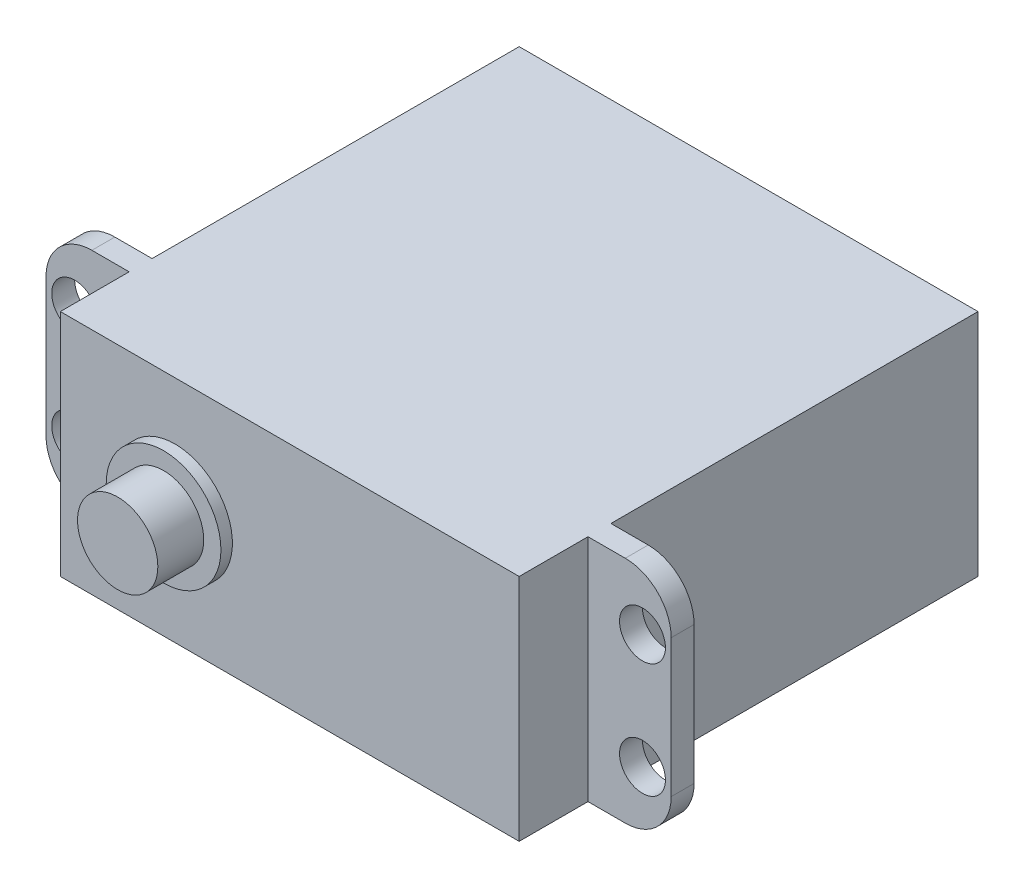
SolidWorks part; units mm, degrees
ref_plane "Front Plane" through (0, 0, 0) normal (0, 0, 1) x (1, 0, 0)
ref_plane "Top Plane" through (0, 0, 0) normal (0, 1, 0) x (1, 0, 0)
ref_plane "Right Plane" through (0, 0, 0) normal (1, 0, 0) x (0, 0, -1)
sketch "Sketch1" plane through (0, 0, 0) normal (0, 0, 1) x (1, 0, 0)
  line L1 (-20, -10) -> (20, -10)
  line L2 (-20, -10) -> (-20, 10)
  line L3 (-20, 10) -> (20, 10)
  line L4 (20, -10) -> (20, 10)
  line L5 (-20, -10) -> (20, 10) construction
  line L6 (-20, 10) -> (20, -10) construction
  point P0 (0, 0)
extrude "Boss-Extrude2" add sketch "Sketch1" along normal blind 40 contours L3 L4 L1 L2
sketch "Sketch2" plane through (20, 0, 0) normal (1, 0, 0) x (0, 0, -1)
  line L0 (-40, -10) -> (-34, -10)
  line L1 (-40, -10) -> (0, -10) construction
  line L2 (-34, -10) -> (-34, 10)
  line L3 (-40, 10) -> (0, 10) construction
  line L4 (-34, 10) -> (-32, 10)
  line L5 (-32, 10) -> (-32, -10)
  line L6 (-32, -10) -> (-34, -10)
extrude "Boss-Extrude3" add sketch "Sketch2" along normal blind 7.25 contours L2 L4 L5 L6
sketch "Sketch3" plane through (0, 0, 34) normal (0, 0, 1) x (1, 0, 0)
  circle A0 centre (24.75, -4.9991) radius 2
  circle A1 centre (24.75, 4.9994) radius 2
extrude "Cut-Extrude1" cut sketch "Sketch3" against normal blind 2 contours A1 | A0
fillet "Fillet3" radius 4 2 edges at (27.25, 10, 33) (27.25, -10, 33)
sketch "Sketch4" plane through (-20, 0, 0) normal (-1, 0, 0) x (0, 0, 1)
  line L0 (40, -10) -> (34, -10)
  line L1 (40, -10) -> (0, -10) construction
  line L2 (34, -10) -> (34, 10)
  line L3 (40, 10) -> (0, 10) construction
  line L4 (34, 10) -> (32, 10)
  line L5 (32, 10) -> (32, -10)
  line L6 (32, -10) -> (34, -10)
extrude "Boss-Extrude4" add sketch "Sketch4" along normal blind 7.25 contours L2 L4 L5 L6
sketch "Sketch5" plane through (0, 0, 34) normal (0, 0, 1) x (1, 0, 0)
  circle A0 centre (-24.75, 5) radius 2
  circle A1 centre (-24.75, -5) radius 2
extrude "Cut-Extrude2" cut sketch "Sketch5" against normal blind 2
fillet "Fillet4" radius 4 2 edges at (-27.25, -10, 33) (-27.25, 10, 33)
sketch "Sketch6" plane through (0, 0, 40) normal (0, 0, 1) x (1, 0, 0)
  circle A1 centre (-10, 0) radius 5
extrude "Boss-Extrude5" add sketch "Sketch6" along normal blind 1
sketch "Sketch7" plane through (0, 0, 41) normal (0, 0, 1) x (1, 0, 0)
  circle A0 centre (-10, 0) radius 3.5
extrude "Boss-Extrude7" add sketch "Sketch7" along normal blind 4
sketch "Sketch9" plane through (0, 0, 0) normal (0, 0, -1) x (-1, 0, 0)
  circle A1 centre (10, 0) radius 5
extrude "Boss-Extrude8" add sketch "Sketch9" along normal blind 1
sketch "Sketch10" plane through (0, 0, -1) normal (0, 0, -1) x (-1, 0, 0)
  circle A0 centre (10, 0) radius 3.5
extrude "Boss-Extrude9" add sketch "Sketch10" along normal blind 4
